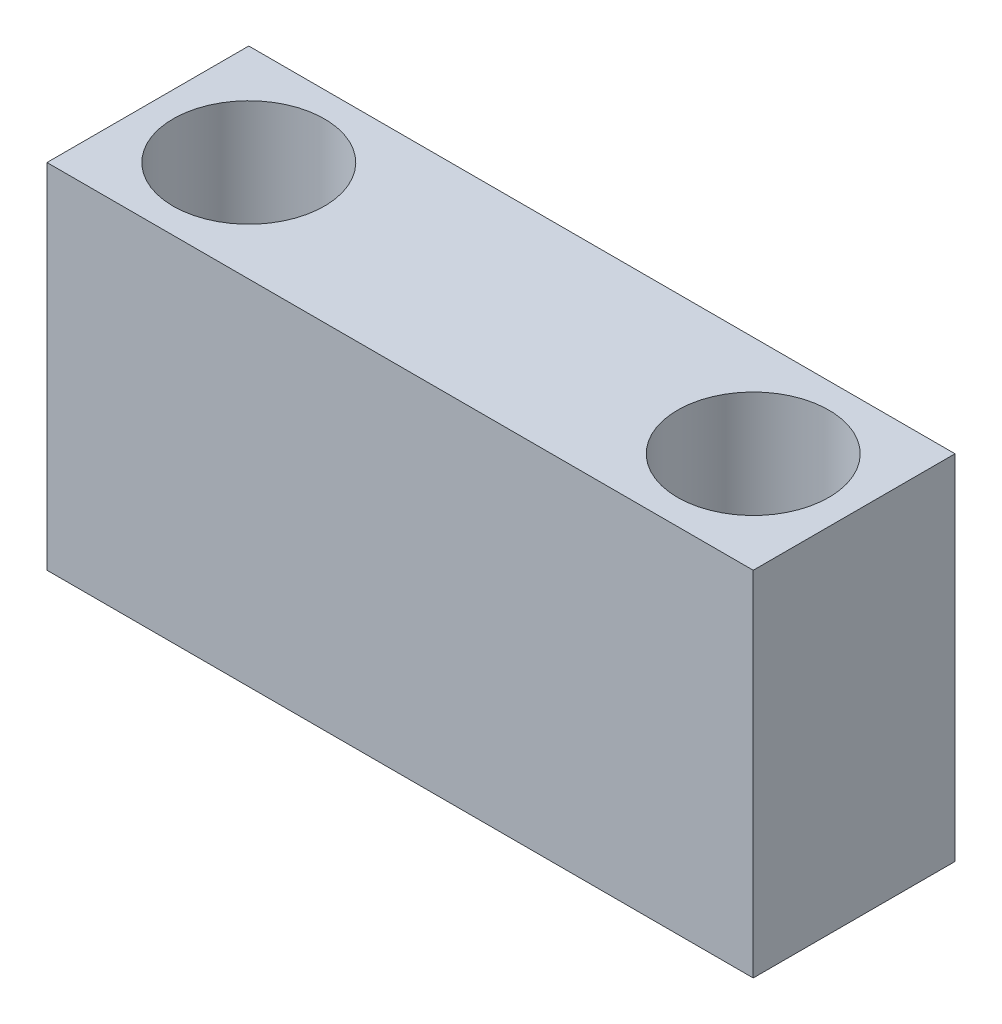
SolidWorks part; units mm, degrees
material "A3钢"
ref_plane "前视基准面" through (0, 0, 0) normal (0, 0, 1) x (1, 0, 0)
ref_plane "上视基准面" through (0, 0, 0) normal (0, 1, 0) x (1, 0, 0)
ref_plane "右视基准面" through (0, 0, 0) normal (1, 0, 0) x (0, 0, -1)
sketch "草图1" plane through (0, 0, 0) normal (0, 0, 1) x (1, 0, 0)
  line L1 (-35, -17.5) -> (35, -17.5)
  line L2 (-35, -17.5) -> (-35, 17.5)
  line L3 (-35, 17.5) -> (35, 17.5)
  line L4 (35, -17.5) -> (35, 17.5)
  line L5 (-35, -17.5) -> (35, 17.5) construction
  line L6 (-35, 17.5) -> (35, -17.5) construction
  point P0 (0, 0)
  dimension "D1" = 35
  dimension "D2" = 70
extrude "凸台-拉伸1" add sketch "草图1" along normal mid plane 20
sketch "草图2" plane through (0, 17.5, 0) normal (0, 1, 0) x (1, 0, 0)
  line L0 (0, 29.153) -> (0, -25.6333) construction
  line L1 (-25, 0) -> (25, 0) construction
  point P5 (0, 0)
  dimension "D1" = 50
hole_wizard "打孔尺寸(%根据)内六角圆柱头螺钉的类型1" positions "3D草图1" profile "草图3" counterbore size "M8" standard "GB" end condition through all
sketch3d "3D草图1"
  point P0 (-25, 17.5, 0)
  point P3 (25, 17.5, 0)
sketch "草图3" plane through (-25, 17.5, 0) normal (1, 0, 0) x (0, 0, 1)
  line L0 (0, 0) -> (0, 35)
  line L1 (0, 35) -> (4.5, 35)
  line L3 (4.5, 35) -> (4.5, 12)
  line L4 (4.5, 12) -> (7.5, 12)
  line L5 (7.5, 12) -> (7.5, 0)
  line L7 (7.5, 0) -> (0, 0)
  line L11 (0, -6.35) -> (0, 107.95) construction
  dimension "通孔孔直径" = 9
  dimension "通孔孔深度" = 35
  dimension "柱形沉头孔直径" = 15
  dimension "柱形沉头孔深度" = 12
